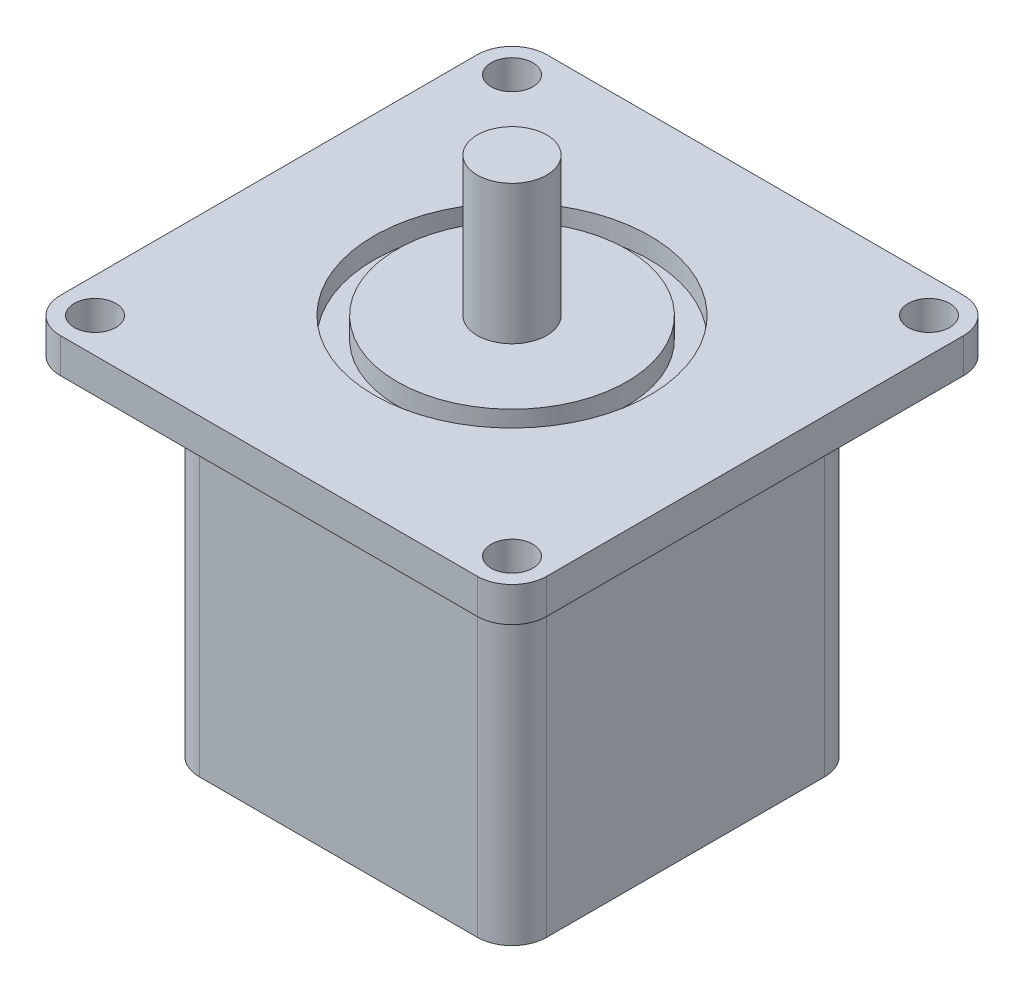
SolidWorks part; units mm, degrees
ref_plane "Front Plane" through (0, 0, 0) normal (0, 0, 1) x (1, 0, 0)
ref_plane "Top Plane" through (0, 0, 0) normal (0, 1, 0) x (1, 0, 0)
ref_plane "Right Plane" through (0, 0, 0) normal (1, 0, 0) x (0, 0, -1)
sketch "Sketch1" plane through (0, 0, 0) normal (0, 1, 0) x (1, 0, 0)
  line L1 (-25, 25) -> (25, 25)
  line L2 (-25, 25) -> (-25, -25)
  line L3 (-25, -25) -> (25, -25)
  line L4 (25, 25) -> (25, -25)
  line L5 (-25, 25) -> (25, -25) construction
  line L6 (-25, -25) -> (25, 25) construction
  point P0 (0, 0)
extrude "Boss-Extrude1" add sketch "Sketch1" along normal blind 50
sketch "Sketch2" plane through (0, 50, 0) normal (0, 1, 0) x (1, 0, 0)
  line L1 (-35, 35) -> (35, 35)
  line L2 (-35, 35) -> (-35, -35)
  line L3 (-35, -35) -> (35, -35)
  line L4 (35, 35) -> (35, -35)
  line L5 (-35, 35) -> (35, -35) construction
  line L6 (-35, -35) -> (35, 35) construction
  line L15 (30, 30) -> (-30, -30) construction
  line L16 (30, -30) -> (-30, 30) construction
  circle A0 centre (-30, 30) radius 3
  circle A1 centre (30, 30) radius 3
  circle A2 centre (-30, -30) radius 3
  circle A3 centre (30, -30) radius 3
  point P0 (0, 0)
  point P6 (0, 0)
  point P15 (0, 0)
  point P16 (0, 0)
  point P19 (0, 0)
  point P20 (0, 0)
  point P21 (0, 0)
extrude "Boss-Extrude2" add sketch "Sketch2" along normal blind 5
fillet "Fillet1" radius 5 4 edges at (-25, 25, -25) (-25, 25, 25) (25, 25, 25) (25, 25, -25)
fillet "Fillet2" radius 5 4 edges at (35, 52.5, -35) (-35, 52.5, -35) (35, 52.5, 35) (-35, 52.5, 35)
sketch "Sketch3" plane through (0, 55, 0) normal (0, 1, 0) x (1, 0, 0)
  circle A0 centre (0, 0) radius 16.5289
  circle A1 centre (0, 0) radius 19.8517
extrude "Cut-Extrude1" cut sketch "Sketch3" against normal blind 3
sketch "Sketch4" plane through (0, 55, 0) normal (0, 1, 0) x (1, 0, 0)
  circle A0 centre (0, 0) radius 5
extrude "Boss-Extrude3" add sketch "Sketch4" along normal blind 20
